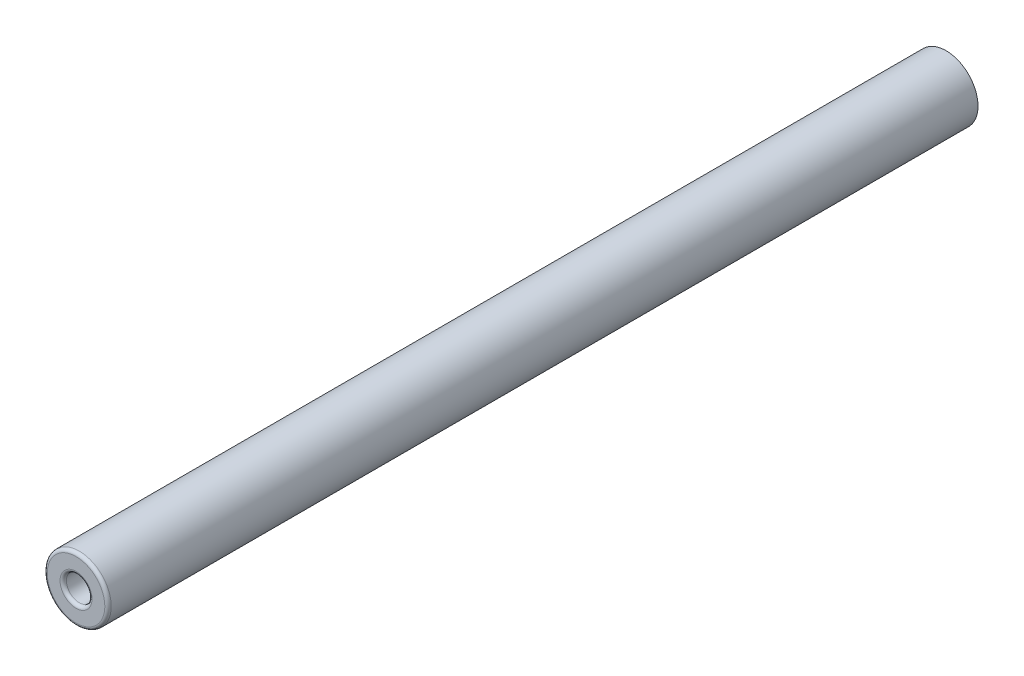
SolidWorks part; units mm, degrees
ref_plane "Front Plane" through (0, 0, 0) normal (0, 0, 1) x (1, 0, 0)
ref_plane "Top Plane" through (0, 0, 0) normal (0, 1, 0) x (1, 0, 0)
ref_plane "Right Plane" through (0, 0, 0) normal (1, 0, 0) x (0, 0, -1)
sketch "Sketch1" plane through (0, 0, 0) normal (0, 0, 1) x (1, 0, 0)
  circle A0 centre (0, 0) radius 2.5
  dimension "D1" = 5
extrude "Boss-Extrude1" add sketch "Sketch1" along normal mid plane 68
sketch "Sketch2" plane through (0, 0, 34) normal (0, 0, 1) x (1, 0, 0)
  circle A0 centre (0, 0) radius 1
  dimension "D1" = 2
extrude "Cut-Extrude1" cut sketch "Sketch2" against normal blind 20
fillet "Fillet1" radius 0.25 2 edges at (2.5, 0, 34) (1, 0, 34)
ref_point "Ponto1"
